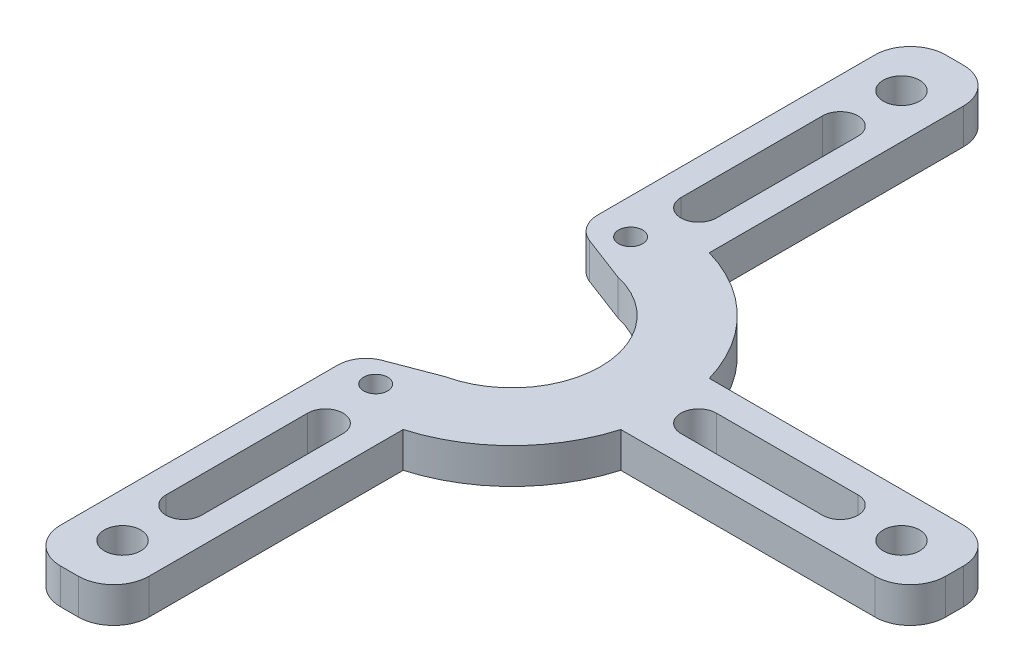
SolidWorks part; units mm, degrees
material "6061-T6 (SS)"
ref_plane "Front Plane" through (0, 0, 0) normal (0, 0, 1) x (1, 0, 0)
ref_plane "Top Plane" through (0, 0, 0) normal (0, 1, 0) x (1, 0, 0)
ref_plane "Right Plane" through (0, 0, 0) normal (1, 0, 0) x (0, 0, -1)
sketch "Sketch1" plane through (0, 0, 0) normal (0, 1, 0) x (1, 0, 0)
  circle A0 centre (0, 0) radius 15.875
  circle A1 centre (0, 0) radius 28.575
  dimension "D1" = 31.75
  dimension "D2" = 57.15
extrude "Boss-Extrude1" add sketch "Sketch1" along normal blind 6.35
sketch "Sketch2" plane through (0, 6.35, 0) normal (0, 1, 0) x (1, 0, 0)
  line L0 (73.025, -7.9375) -> (25.4, -7.9375)
  line L1 (79.375, -1.5875) -> (79.375, 1.5875)
  line L2 (25.4, -7.9375) -> (25.4, 7.9375)
  line L3 (73.025, 7.9375) -> (25.4, 7.9375)
  line L4 (79.375, -7.9375) -> (25.4, 7.9375) construction
  line L5 (25.4, -7.9375) -> (79.375, 7.9375) construction
  line L6 (0, -55) -> (0, 55) construction
  line L7 (52.3875, 0) -> (0, 0) construction
  line L8 (58.8708, 0) -> (33.4708, 0) construction
  line L9 (58.8708, -3.175) -> (33.4708, -3.175)
  line L10 (58.8708, 3.175) -> (33.4708, 3.175)
  arc A0 (79.375, -1.5875) -> (73.025, -7.9375) centre (73.025, -1.5875) cw
  arc A1 (79.375, 1.5875) -> (73.025, 7.9375) centre (73.025, 1.5875) ccw
  arc A2 (58.8708, -3.175) -> (58.8708, 3.175) centre (58.8708, 0) ccw
  arc A3 (33.4708, 3.175) -> (33.4708, -3.175) centre (33.4708, 0) ccw
  point P1 (52.3875, 0)
  point P18 (46.1708, 0)
  point P23 (48.2435, 0)
  point P24 (52.3875, 0)
  point P25 (0, 0)
  point P26 (52.3875, 0)
  dimension "D4" = 6.35
  dimension "D1" = 53.975
  dimension "D2" = 25.4
  dimension "D3" = 15.875
  dimension "D5" = 25.4
  dimension "D6" = 6.35
extrude "Boss-Extrude2" add sketch "Sketch2" against normal blind 6.35
hole_wizard "F (0.257) Diameter Hole1" positions "Sketch3" profile "Sketch4" hole size "F" standard "ANSI Inch" end condition through all
sketch "Sketch3" plane through (0, 6.35, 0) normal (0, 1, 0) x (1, 0, 0)
  line L0 (0, 0) -> (69.85, 0) construction
  point P0 (69.85, 0)
  dimension "D1" = 69.85
sketch "Sketch4" plane through (69.85, 6.35, 0) normal (1, 0, 0) x (0, 0, 1)
  line L0 (0, 0) -> (0, 6.35)
  line L1 (0, 6.35) -> (3.2639, 6.35)
  line L2 (3.2639, 6.35) -> (3.2639, 0)
  line L5 (3.2639, 0) -> (0, 0)
  line L11 (0, -6.35) -> (0, 107.95) construction
  dimension "Thru Hole Dia." = 6.5278
  dimension "Thru Hole Depth" = 6.35
pattern_circular "CirPattern1" count 4 over 360 about axis through (0, 0, 0) along (0, 1, 0) of "Boss-Extrude2", "F (0.257) Diameter Hole1"
sketch "Sketch5" plane through (0, 6.35, 0) normal (0, 1, 0) x (1, 0, 0)
  line L4 (0, 0) -> (-9.9657, 0) construction
  line L6 (-7.9375, 19.8304) -> (-7.9375, 27.4504)
  line L8 (-88.1528, 52.5366) -> (-7.9375, 52.5366)
  line L10 (69.85, 0) -> (-143.7235, 0) construction
  line L11 (-88.1528, 52.5366) -> (-88.1528, -52.5366)
  line L12 (-7.9375, 27.4504) -> (-7.9375, 52.5366)
  line L13 (-7.9375, 19.8304) -> (3.4925, 19.8304) construction
  line L14 (3.4925, 19.8304) -> (3.4925, 15.4861) construction
  line L15 (3.4925, 15.4861) -> (-7.9375, 19.8304)
  line L16 (-7.9375, 73.025) -> (-7.9375, 27.4504) construction
  line L17 (3.4925, 15.4861) -> (3.4925, -15.4861)
  line L18 (-7.9375, -27.4504) -> (-7.9375, -52.5366)
  line L19 (-88.1528, -52.5366) -> (-7.9375, -52.5366)
  line L20 (3.4925, -19.8304) -> (3.4925, -15.4861) construction
  line L21 (-7.9375, -19.8304) -> (3.4925, -19.8304) construction
  line L22 (3.4925, -15.4861) -> (-7.9375, -19.8304)
  line L23 (-7.9375, -19.8304) -> (-7.9375, -27.4504)
  circle A0 centre (0, 0) radius 15.875 construction
  arc A1 (-7.9375, 27.4504) -> (-27.4504, 7.9375) centre (0, 0) ccw construction
  point P5 (-9.9657, 0)
  point P7 (3.3062, 14.2259)
  point P22 (3.3062, 21.1004)
  point P24 (-88.1528, 0)
  point P28 (3.4925, 0)
  dimension "D1" = 90
  dimension "D2" = 7.62
  dimension "D3" = 11.43
extrude "Cut-Extrude1" cut sketch "Sketch5" against normal through all
fillet "Fillet1" radius 5.08 2 edges at (-7.9375, 3.175, 19.8304) (-7.9375, 3.175, -19.8304)
sketch "Sketch6" plane through (0, 6.35, 0) normal (0, 1, 0) x (1, 0, 0)
  line L0 (-7.9375, 73.025) -> (-7.9375, 23.3342) construction
  line L1 (0, 0) -> (-30.3402, 0) construction
  circle A0 centre (-1.5875, 22.86) radius 2.1526
  circle A1 centre (-1.5875, -22.86) radius 2.1526
  dimension "D1" = 4.3053
  dimension "D2" = 22.86
  dimension "D3" = 6.35
extrude "Cut-Extrude2" cut sketch "Sketch6" against normal through all
